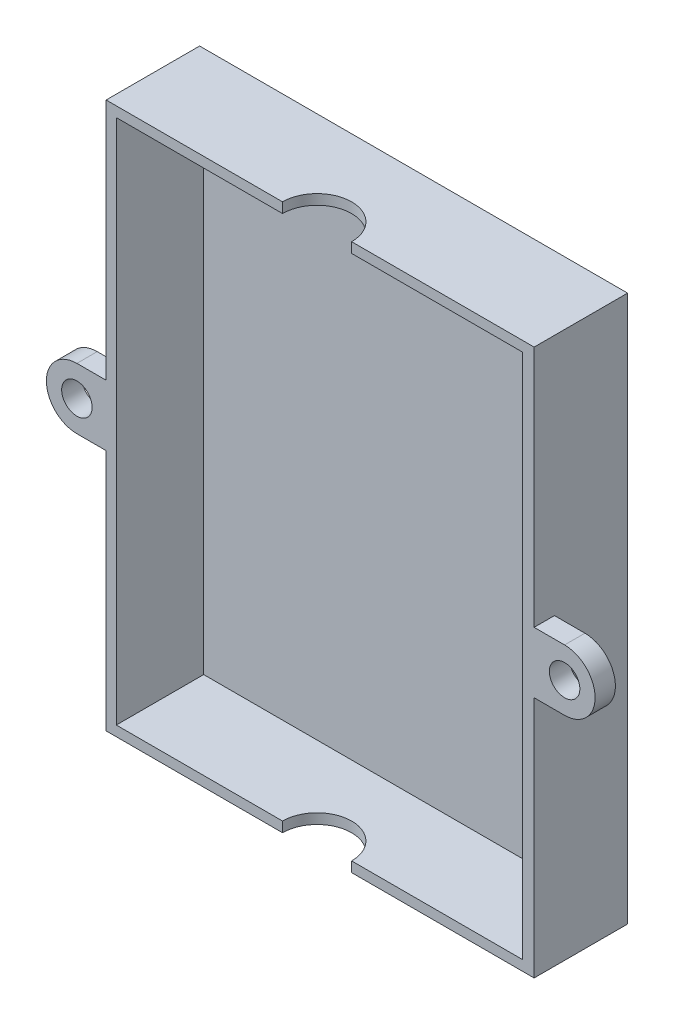
SolidWorks part; units mm, degrees
ref_plane "Front Plane" through (0, 0, 0) normal (0, 0, 1) x (1, 0, 0)
ref_plane "Top Plane" through (0, 0, 0) normal (0, 1, 0) x (1, 0, 0)
ref_plane "Right Plane" through (0, 0, 0) normal (1, 0, 0) x (0, 0, -1)
sketch "Sketch2" plane through (0, 0, 0) normal (0, 0, 1) x (-1, 0, 0)
  line L1 (98.3509, 136.1445) -> (-101.6491, 136.1445)
  line L2 (98.3509, 136.1445) -> (98.3509, -122.7351)
  line L3 (98.3509, -122.7351) -> (-101.6491, -122.7351)
  line L4 (-101.6491, 136.1445) -> (-101.6491, -122.7351)
  line L5 (98.3509, 136.1445) -> (-101.6491, -122.7351) construction
  line L6 (98.3509, -122.7351) -> (-101.6491, 136.1445) construction
  point P5 (0, 0)
  point P6 (0, 0)
  point P7 (0, 0)
  point P8 (0, 0)
  point P9 (92.7552, -98.7576)
  point P10 (0, 0)
extrude "Boss-Extrude1" add sketch "Sketch2" along normal blind 3
sketch "Sketch6" plane through (0, 0, 3) normal (0, 0, 1) x (1, 0, 0)
  line L0 (-98.3509, 122.7351) -> (101.6491, 122.7351)
  line L1 (101.6491, 122.7351) -> (101.6491, -136.1445)
  line L2 (101.6491, -136.1445) -> (-98.3509, -136.1445)
  line L3 (-98.3509, -136.1445) -> (-98.3509, 122.7351)
  line L6 (-98.3509, 127.7351) -> (-103.3509, 127.7351)
  line L7 (-103.3509, 127.7351) -> (-103.3509, 122.7351)
  line L12 (-98.3509, 127.7351) -> (107.2527, 127.7351)
  line L13 (107.2527, 127.7351) -> (107.2527, -141.1445)
  line L14 (107.2527, -141.1445) -> (-103.3509, -141.1445)
  line L15 (-103.3509, -141.1445) -> (-103.3509, 122.7351)
  dimension "D1" = 5
extrude "Boss-Extrude2" add sketch "Sketch6" along normal blind 43 and the other way blind 3
sketch "Sketch7" plane through (0, -141.1445, 0) normal (0, -1, 0) x (1, 0, 0)
  line L1 (-103.3509, 46) -> (107.2527, 46) construction
  line L2 (0.4527, 46) -> (107.2527, 46)
  circle A0 centre (0.4527, 46) radius 17
extrude "Cut-Extrude1" cut sketch "Sketch7" against normal through all both and the other way through all contours A0
sketch "Sketch9" plane through (0, 0, 46) normal (0, 0, 1) x (1, 0, 0)
  line L10 (107.2527, 8.2953) -> (107.2527, -6.7047)
  line L11 (107.2527, -21.7047) -> (107.2527, -6.7047)
  line L12 (122.2527, 8.2953) -> (107.2527, 8.2953)
  line L13 (122.2527, -21.7047) -> (107.2527, -21.7047)
  line L15 (-102.7473, -21.7047) -> (-102.7473, -6.7047)
  line L16 (-102.7473, 8.2953) -> (-102.7473, -6.7047)
  line L17 (-117.7473, -21.7047) -> (-102.7473, -21.7047)
  line L18 (-117.7473, 8.2953) -> (-102.7473, 8.2953)
  arc A4 (122.2527, -21.7047) -> (122.2527, 8.2953) centre (122.2527, -6.7047) ccw
  circle A5 centre (122.2527, -6.7047) radius 7.5
  arc A6 (-117.7473, 8.2953) -> (-117.7473, -21.7047) centre (-117.7473, -6.7047) ccw
  circle A7 centre (-117.7473, -6.7047) radius 7.5
extrude "Boss-Extrude3" add sketch "Sketch9" against normal blind 10
